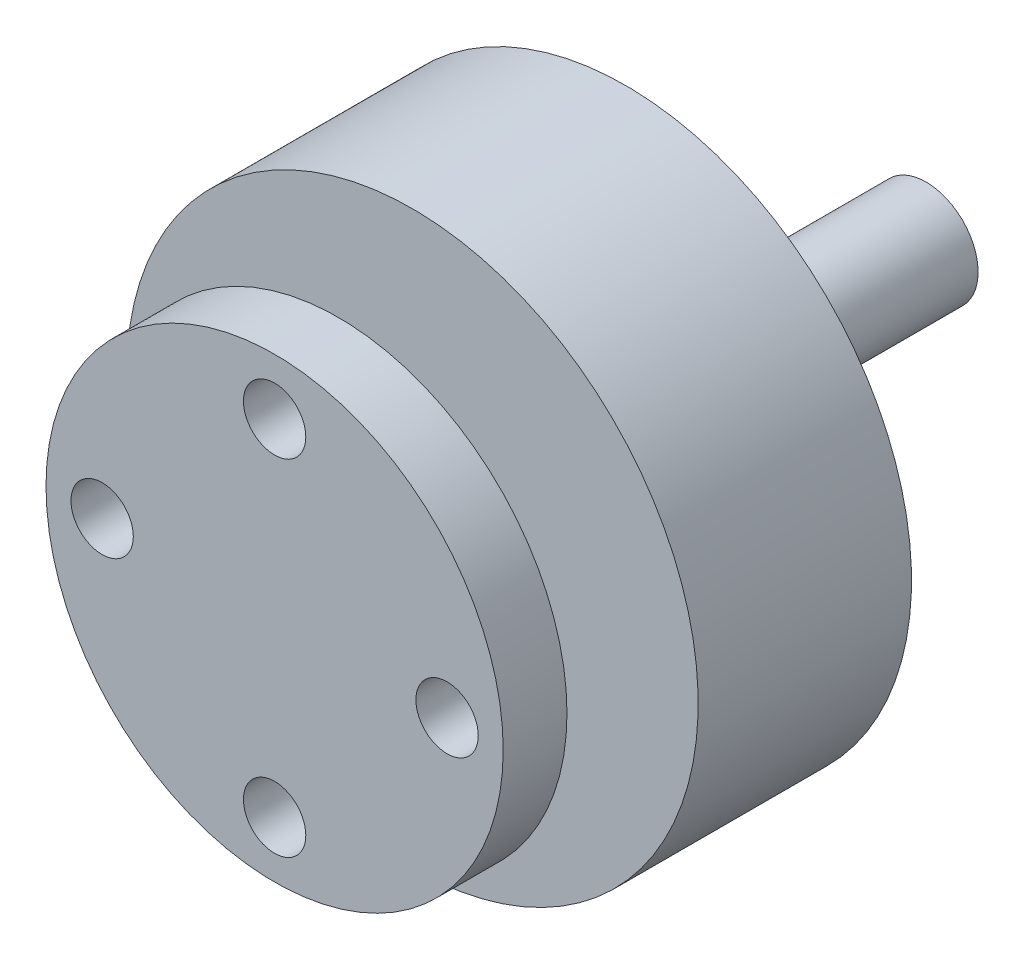
SolidWorks part; units mm, degrees
ref_plane "Front" through (0, 0, 0) normal (0, 0, 1) x (1, 0, 0)
ref_plane "Top" through (0, 0, 0) normal (0, 1, 0) x (1, 0, 0)
ref_plane "Right" through (0, 0, 0) normal (1, 0, 0) x (0, 0, -1)
sketch "Sketch1" plane through (0, 0, 0) normal (0, 1, 0) x (1, 0, 0)
  line L0 (0, 0) -> (11, 0)
  line L1 (11, 0) -> (11, 3.0682)
  line L2 (11, 3.0682) -> (3.7386, 3.0682)
  line L3 (3.7386, 3.0682) -> (3.7386, 6.6313)
  line L4 (3.7386, 6.6313) -> (13.75, 6.6313)
  line L5 (13.75, 6.6313) -> (13.75, 16.8963)
  line L6 (13.75, 16.8963) -> (7.8198, 19.35)
  line L7 (7.8198, 19.35) -> (2.5, 19.35)
  line L8 (2.5, 19.35) -> (2.5, 31.35)
  line L9 (2.5, 31.35) -> (0, 31.35)
  line L10 (0, 31.35) -> (0, 0) construction
  line L11 (0, 0) -> (0, 31.35)
  point P9 (11.1481, 19.35)
  point P14 (13.4386, 3.0682)
  point P15 (13.75, 6.6313)
  point P16 (11.6571, 19.35)
  point P17 (13.75, 16.8963)
  point P18 (7.8198, 19.35)
  dimension "D1" = 12
  dimension "D2" = 31.35
  dimension "D3" = 2.5
  dimension "D4" = 27.5
  dimension "D5" = 22
revolve "Revolve1" add sketch "Sketch1" angle 360 about L10
sketch "Sketch2" plane through (0, 0, 0) normal (0, 0, 1) x (1, 0, 0)
  circle A0 centre (0, 0) radius 8.2989 construction
  circle A1 centre (8.2989, 0) radius 1.5
  circle A2 centre (0, -8.2989) radius 1.5
  circle A3 centre (-8.2989, 0) radius 1.5
  circle A4 centre (0, 8.2989) radius 1.5
  point P14 (0, 0)
  dimension "D1" = 3
  dimension "D2" = 4
extrude "Cut-Extrude1" cut sketch "Sketch2" against normal blind 5
